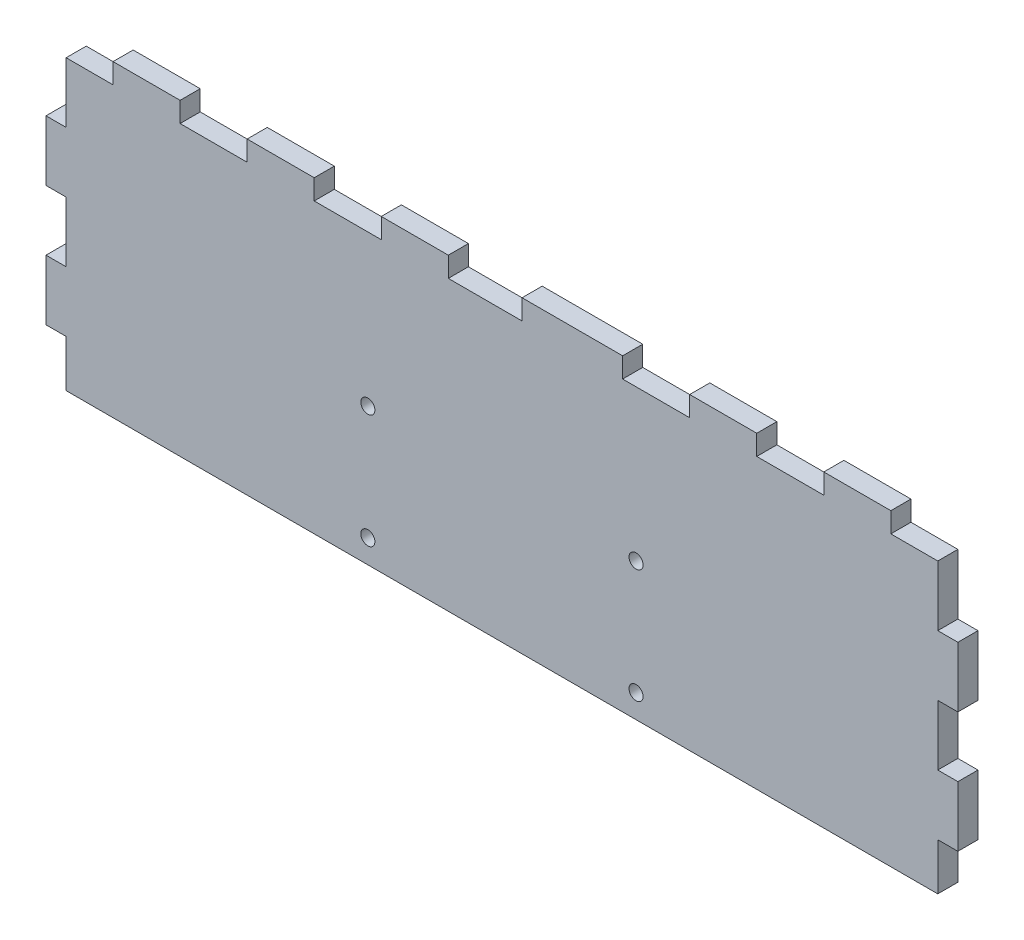
SolidWorks part; units mm, degrees
ref_plane "Front Plane" through (0, 0, 0) normal (0, 0, 1) x (1, 0, 0)
ref_plane "Top Plane" through (0, 0, 0) normal (0, 1, 0) x (1, 0, 0)
ref_plane "Right Plane" through (0, 0, 0) normal (1, 0, 0) x (0, 0, -1)
sketch "Sketch1" plane through (0, 0, 0) normal (0, 0, 1) x (1, 0, 0)
  line L4 (0, 0) -> (136, 0)
  line L5 (136, 0) -> (136, 46)
  line L6 (136, 46) -> (0, 46)
  line L7 (0, 46) -> (0, 0)
  line L8 (0, 0) -> (136, 0)
  line L9 (136, 0) -> (136, 46)
  line L10 (136, 46) -> (0, 46)
  line L11 (0, 46) -> (0, 0)
  circle A0 centre (88, 20.5) radius 1.05 construction
  circle A1 centre (48, 20.5) radius 1.05 construction
  circle A2 centre (48, 3.5) radius 1.05 construction
  circle A3 centre (88, 3.5) radius 1.05 construction
  circle A4 centre (88, 20.5) radius 1.05
  circle A5 centre (48, 20.5) radius 1.05
  circle A6 centre (48, 3.5) radius 1.05
  circle A7 centre (88, 3.5) radius 1.05
  dimension "D1" = 0
extrude "Boss-Extrude1" add sketch "Sketch1" along normal blind 3
sketch "Sketch4" plane through (0, 0, 3) normal (0, 0, 1) x (1, 0, 0)
  line L0 (136, 0) -> (136, 7) construction
  line L1 (136, 7) -> (133, 7) construction
  line L2 (133, 7) -> (133, 0) construction
  line L3 (133, 0) -> (136, 0) construction
  line L4 (133, 25) -> (133, 16) construction
  line L5 (133, 16) -> (136, 16) construction
  line L6 (136, 16) -> (136, 25) construction
  line L7 (136, 25) -> (133, 25) construction
  line L8 (136, 34) -> (136, 43) construction
  line L9 (133, 34) -> (136, 34) construction
  line L10 (133, 43) -> (133, 34) construction
  line L11 (136, 43) -> (133, 43) construction
  line L12 (126, 43) -> (136, 43) construction
  line L13 (126, 46) -> (126, 43) construction
  line L14 (136, 46) -> (126, 46) construction
  line L15 (136, 43) -> (136, 46) construction
  line L16 (40, 43) -> (50, 43) construction
  line L17 (50, 43) -> (50, 46) construction
  line L18 (50, 46) -> (40, 46) construction
  line L19 (40, 46) -> (40, 43) construction
  line L20 (60, 43) -> (71, 43) construction
  line L21 (71, 43) -> (71, 46) construction
  line L22 (71, 46) -> (60, 46) construction
  line L23 (60, 46) -> (60, 43) construction
  line L24 (86, 43) -> (96, 43) construction
  line L25 (96, 43) -> (96, 46) construction
  line L26 (96, 46) -> (86, 46) construction
  line L27 (86, 46) -> (86, 43) construction
  line L28 (106, 46) -> (106, 43) construction
  line L29 (106, 43) -> (116, 43) construction
  line L30 (116, 43) -> (116, 46) construction
  line L31 (116, 46) -> (106, 46) construction
  line L32 (0, 25) -> (0, 16) construction
  line L33 (0, 16) -> (3, 16) construction
  line L34 (3, 16) -> (3, 25) construction
  line L35 (3, 25) -> (0, 25) construction
  line L36 (0, 43) -> (10, 43) construction
  line L37 (10, 43) -> (10, 46) construction
  line L38 (10, 46) -> (0, 46) construction
  line L39 (0, 46) -> (0, 43) construction
  line L40 (0, 43) -> (0, 34) construction
  line L41 (0, 34) -> (3, 34) construction
  line L42 (3, 34) -> (3, 43) construction
  line L43 (3, 43) -> (0, 43) construction
  line L44 (30, 43) -> (30, 46) construction
  line L45 (30, 46) -> (20, 46) construction
  line L46 (20, 46) -> (20, 43) construction
  line L47 (20, 43) -> (30, 43) construction
  line L48 (0, 7) -> (0, 0) construction
  line L49 (0, 0) -> (3, 0) construction
  line L50 (3, 0) -> (3, 7) construction
  line L51 (3, 7) -> (0, 7) construction
  line L52 (136, 0) -> (136, 7)
  line L53 (136, 7) -> (133, 7)
  line L54 (133, 7) -> (133, 0)
  line L55 (133, 0) -> (136, 0)
  line L56 (133, 25) -> (133, 16)
  line L57 (133, 16) -> (136, 16)
  line L58 (136, 16) -> (136, 25)
  line L59 (136, 25) -> (133, 25)
  line L60 (136, 34) -> (136, 43)
  line L61 (133, 34) -> (136, 34)
  line L62 (133, 43) -> (133, 34)
  line L63 (136, 43) -> (133, 43)
  line L64 (126, 43) -> (136, 43)
  line L65 (126, 46) -> (126, 43)
  line L66 (136, 46) -> (126, 46)
  line L67 (136, 43) -> (136, 46)
  line L68 (40, 43) -> (50, 43)
  line L69 (50, 43) -> (50, 46)
  line L70 (50, 46) -> (40, 46)
  line L71 (40, 46) -> (40, 43)
  line L72 (60, 43) -> (71, 43)
  line L73 (71, 43) -> (71, 46)
  line L74 (71, 46) -> (60, 46)
  line L75 (60, 46) -> (60, 43)
  line L76 (86, 43) -> (96, 43)
  line L77 (96, 43) -> (96, 46)
  line L78 (96, 46) -> (86, 46)
  line L79 (86, 46) -> (86, 43)
  line L80 (106, 46) -> (106, 43)
  line L81 (106, 43) -> (116, 43)
  line L82 (116, 43) -> (116, 46)
  line L83 (116, 46) -> (106, 46)
  line L84 (0, 25) -> (0, 16)
  line L85 (0, 16) -> (3, 16)
  line L86 (3, 16) -> (3, 25)
  line L87 (3, 25) -> (0, 25)
  line L88 (0, 43) -> (10, 43)
  line L89 (10, 43) -> (10, 46)
  line L90 (10, 46) -> (0, 46)
  line L91 (0, 46) -> (0, 43)
  line L92 (0, 43) -> (0, 34)
  line L93 (0, 34) -> (3, 34)
  line L94 (3, 34) -> (3, 43)
  line L95 (3, 43) -> (0, 43)
  line L96 (30, 43) -> (30, 46)
  line L97 (30, 46) -> (20, 46)
  line L98 (20, 46) -> (20, 43)
  line L99 (20, 43) -> (30, 43)
  line L100 (0, 7) -> (0, 0)
  line L101 (0, 0) -> (3, 0)
  line L102 (3, 0) -> (3, 7)
  line L103 (3, 7) -> (0, 7)
  line M3 (0, 46) -> (0, 0)
  line M4 (0, 0) -> (136, 0)
  line M5 (136, 0) -> (136, 46)
  line M6 (136, 46) -> (0, 46)
extrude "Cut-Extrude1" cut sketch "Sketch4" against normal up to next contours L88 L89 M6 M3 | L93 L94 L88 M3 | L86 L87 L85 M3 | L102 L103 M3 M4 | L98 L99 L96 M6 | L71 L68 L69 M6 | L75 L72 L73 M6 | L79 L76 L77 M6 | L81 L82 L80 M6 | L65 L64 L63 M6 M5 | L63 L62 L61 M5 | L59 L56 L57 M5 | L53 L54 M4 M5
